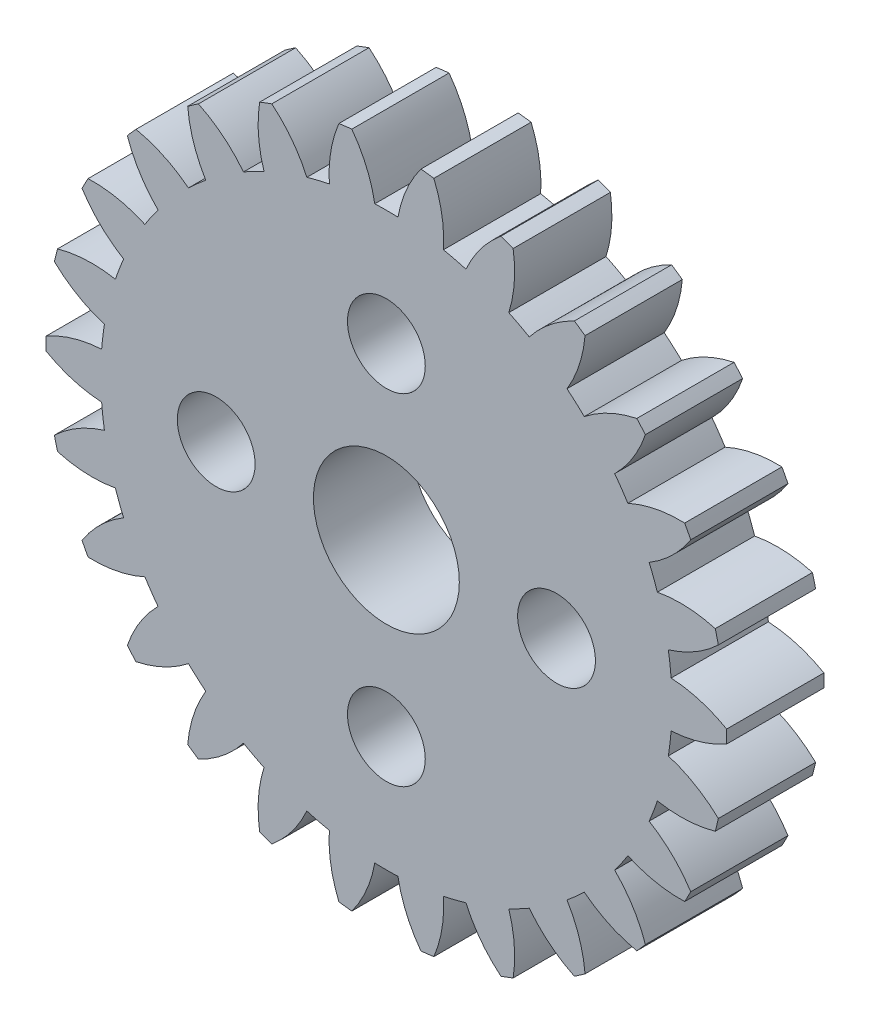
SolidWorks part; units mm, degrees
material "鑄碳鋼"
ref_plane "前基準面" through (0, 0, 0) normal (0, 0, 1) x (1, 0, 0)
ref_plane "上基準面" through (0, 0, 0) normal (0, 1, 0) x (1, 0, 0)
ref_plane "右基準面" through (0, 0, 0) normal (1, 0, 0) x (0, 0, -1)
sketch "草圖1" plane through (0, 0, 0) normal (0, 0, 1) x (1, 0, 0)
  circle A0 centre (0, 0) radius 14
  dimension "D1" = 28
extrude "填料-伸長1" add sketch "草圖1" along normal blind 4
sketch "草圖2" plane through (0, 0, 4) normal (0, 0, 1) x (1, 0, 0)
  line L0 (-1.4216, 13.9276) -> (0, 0) construction
  line L1 (1.4216, 13.9276) -> (0, 0) construction
  line L2 (0, 0) -> (0.477, 11.7403) construction
  line L3 (-0.477, 11.7403) -> (0, 0) construction
  arc A0 (-1.4216, 13.9276) -> (1.4216, 13.9276) centre (0, 0) cw
  circle A1 centre (0, 0) radius 14 construction
  arc A2 (-0.477, 11.7403) -> (0.477, 11.7403) centre (0, 0) cw
  arc A3 (-1.4216, 13.9276) -> (-0.477, 11.7403) centre (-5.5962, 10.8272) cw
  arc A4 (1.4216, 13.9276) -> (0.477, 11.7403) centre (5.5962, 10.8272) ccw
  circle A5 centre (0, 0) radius 13 construction
  point P10 (0, 11.75)
  point P11 (0, 14)
  dimension "D1" = 5.2
  dimension "D2" = 5.2
  dimension "D5" = 11.75
  dimension "D6" = 26
  dimension "D3" = 4.653
  dimension "D4" = 11.656
extrude "除料-伸長1" cut sketch "草圖2" against normal up to next (4 mm away)
pattern_circular "環狀複製排列1" count 26 over 360 about axis through (0, 0, 0) along (0, 0, 1) of "除料-伸長1"
sketch "草圖3" plane through (0, 0, 4) normal (0, 0, 1) x (1, 0, 0)
  circle A0 centre (0, 0) radius 3
  circle A1 centre (0, 0) radius 7 construction
  circle A2 centre (0, 7) radius 1.6
  circle A3 centre (7, 0) radius 1.6
  circle A4 centre (0, -7) radius 1.6
  circle A5 centre (-7, 0) radius 1.6
  dimension "D1" = 6
  dimension "D2" = 14
  dimension "D3" = 3.2
  dimension "D5" = 90
  dimension "D4" = 4
extrude "除料-伸長2" cut sketch "草圖3" against normal up to next
